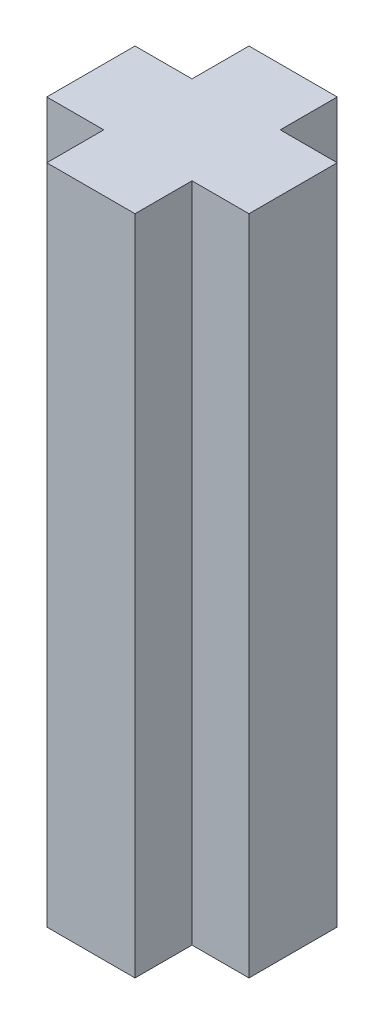
SolidWorks part; units mm, degrees
ref_plane "Front Plane" through (0, 0, 0) normal (0, 0, 1) x (1, 0, 0)
ref_plane "Top Plane" through (0, 0, 0) normal (0, 1, 0) x (1, 0, 0)
ref_plane "Right Plane" through (0, 0, 0) normal (1, 0, 0) x (0, 0, -1)
sketch "Sketch1" plane through (0, 0, 0) normal (0, 1, 0) x (1, 0, 0)
  line L12 (2.2807, -0.9522) -> (0.9894, -0.9522)
  line L13 (2.2807, 1.0478) -> (2.2807, -0.9522)
  line L14 (0.9894, 1.0478) -> (2.2807, 1.0478)
  line L15 (0.9894, 2.3391) -> (0.9894, 1.0478)
  line L16 (-1.0106, 2.3391) -> (0.9894, 2.3391)
  line L17 (-1.0106, 1.0478) -> (-1.0106, 2.3391)
  line L18 (-2.3019, 1.0478) -> (-1.0106, 1.0478)
  line L19 (-2.3019, -0.9522) -> (-2.3019, 1.0478)
  line L20 (-1.0106, -0.9522) -> (-2.3019, -0.9522)
  line L21 (-1.0106, -2.2435) -> (-1.0106, -0.9522)
  line L22 (0.9894, -2.2435) -> (-1.0106, -2.2435)
  line L23 (0.9894, -0.9522) -> (0.9894, -2.2435)
extrude "Boss-Extrude1" add sketch "Sketch1" along normal blind 15
